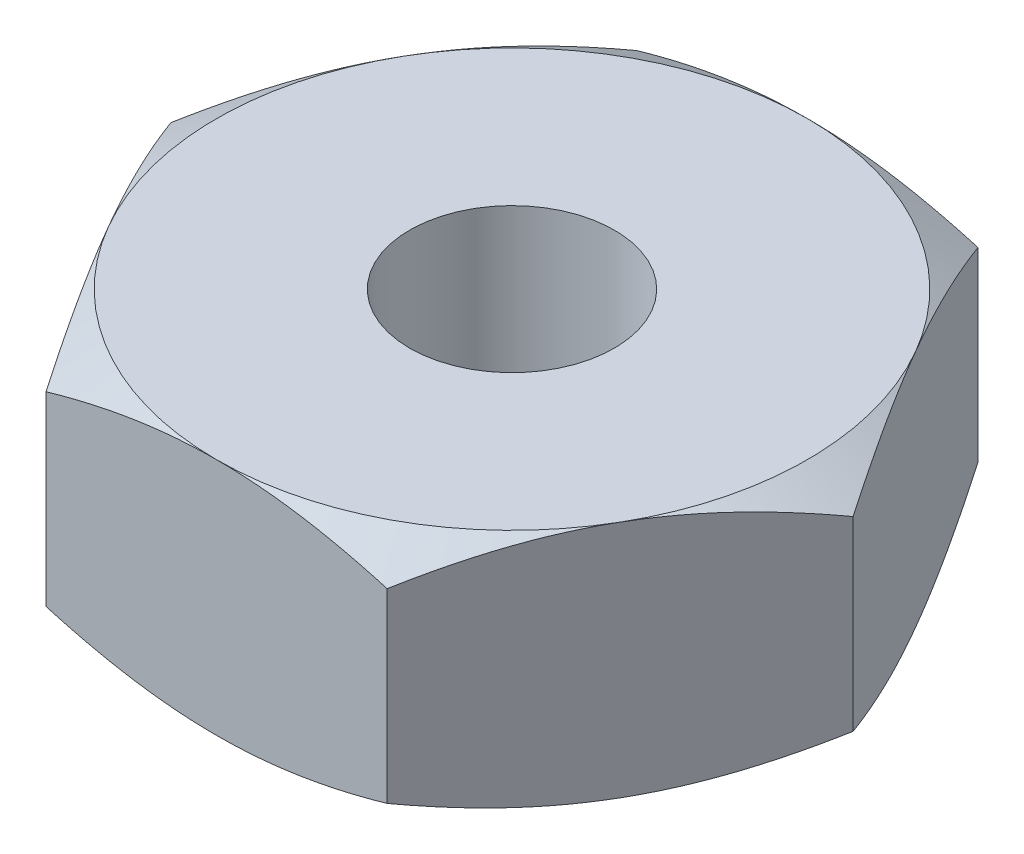
SolidWorks part; units mm, degrees
ref_plane "Front Plane" through (0, 0, 0) normal (0, 0, 1) x (1, 0, 0)
ref_plane "Top Plane" through (0, 0, 0) normal (0, 1, 0) x (1, 0, 0)
ref_plane "Right Plane" through (0, 0, 0) normal (1, 0, 0) x (0, 0, -1)
sketch "Sketch1" plane through (0, 0, 0) normal (0, 1, 0) x (1, 0, 0)
  line L1 (-10, 0) -> (-5, -8.6603)
  line L2 (-5, -8.6603) -> (5, -8.6603)
  line L3 (5, -8.6603) -> (10, 0)
  line L4 (10, 0) -> (5, 8.6603)
  line L5 (5, 8.6603) -> (-5, 8.6603)
  line L6 (-5, 8.6603) -> (-10, 0)
  circle A0 centre (0, 0) radius 8.6603 construction
  dimension "D1" = 20
extrude "Boss-Extrude1" add sketch "Sketch1" along normal mid plane 7
sketch "Sketch2" plane through (0, 3.5, 0) normal (0, 1, 0) x (1, 0, 0)
  circle A0 centre (0, 0) radius 8.6603
extrude "Cut-Extrude1" cut sketch "Sketch2" against normal blind 7 draft 60 flip side to cut
mirror "Mirror1" about plane through (0, 0, 0) normal (0, 1, 0) of "Cut-Extrude1"
sketch "Sketch3" plane through (0, 3.5, 0) normal (0, 1, 0) x (1, 0, 0)
  circle A0 centre (0, 0) radius 3
  dimension "D1" = 6
extrude "Cut-Extrude2" cut sketch "Sketch3" against normal through all
